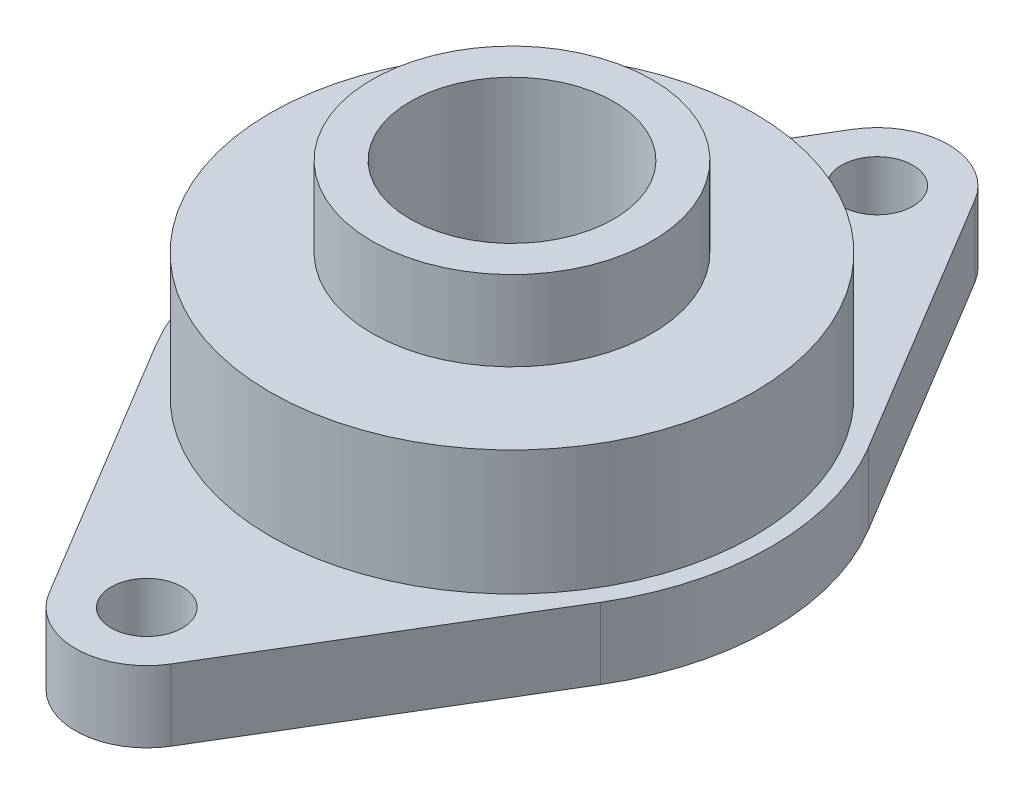
SolidWorks part; units mm, degrees
ref_plane "Front Plane" through (0, 0, 0) normal (0, 0, 1) x (1, 0, 0)
ref_plane "Top Plane" through (0, 0, 0) normal (0, 1, 0) x (1, 0, 0)
ref_plane "Right Plane" through (0, 0, 0) normal (1, 0, 0) x (0, 0, -1)
sketch "Sketch1" plane through (0, 0, 0) normal (0, 1, 0) x (1, 0, 0)
  line L0 (0, 85.75) -> (0, -85.75) construction
  line L1 (-51, 85.75) -> (51, 85.75)
  line L2 (-51, 85.75) -> (-51, -85.75)
  line L3 (-51, -85.75) -> (51, -85.75)
  line L4 (51, 85.75) -> (51, -85.75)
  line L5 (-51, 85.75) -> (51, -85.75) construction
  line L6 (-51, -85.75) -> (51, 85.75) construction
  line L7 (-51, 0) -> (51, 0) construction
  line L8 (-43.6959, 26.2997) -> (-11.9949, 78.9695)
  line L9 (11.9949, 78.9695) -> (43.6959, 26.2997)
  line L10 (-43.6959, -26.2997) -> (-11.9949, -78.9695)
  line L11 (11.9949, -78.9695) -> (43.6959, -26.2997)
  circle A0 centre (0, 71.75) radius 7
  circle A1 centre (0, -71.75) radius 7
  circle A2 centre (0, 0) radius 20
  circle A3 centre (0, 71.75) radius 14
  circle A4 centre (0, -71.75) radius 14
  circle A5 centre (0, 0) radius 51
  point P0 (0, 0)
  dimension "D2" = 14
  dimension "D5" = 40
  dimension "D1" = 171.5
  dimension "D3" = 143.5
  dimension "D4" = 102
extrude "Boss-Extrude1" add sketch "Sketch1" along normal blind 14 contours A3 A0 | A5 L9 A3 L8 | A5 L10 A4 L11 | A4 A1 | A5 A2
sketch "Sketch2" plane through (0, 14, 0) normal (0, 1, 0) x (1, 0, 0)
  circle A0 centre (0, 0) radius 47.5
  circle A2 centre (0, 0) radius 20
  circle A3 centre (0, 0) radius 20 construction
  dimension "D1" = 95
extrude "Boss-Extrude2" add sketch "Sketch2" along normal offset from surface (24.5 mm away) 38.5 up to face at (0, 0, 0)
sketch "Sketch3" plane through (0, 38.5, 0) normal (0, 1, 0) x (1, 0, 0)
  circle A0 centre (0, 0) radius 20 construction
  circle A1 centre (0, 0) radius 20
  circle A2 centre (0, 0) radius 27.5
  dimension "D1" = 55
extrude "Boss-Extrude3" add sketch "Sketch3" along normal offset from surface (15.7 mm away) 54.2 up to face at (0, 0, 0)
